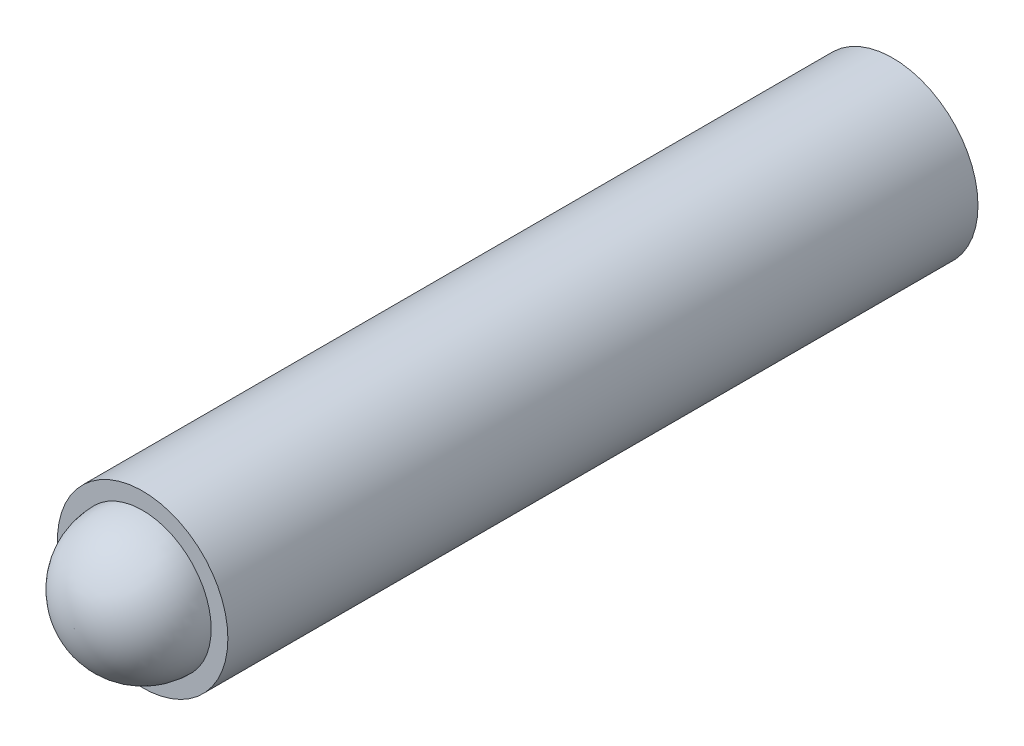
SolidWorks part; units mm, degrees
ref_plane "Front Plane" through (0, 0, 0) normal (0, 0, 1) x (1, 0, 0)
ref_plane "Top Plane" through (0, 0, 0) normal (0, 1, 0) x (1, 0, 0)
ref_plane "Right Plane" through (0, 0, 0) normal (1, 0, 0) x (0, 0, -1)
sketch "Sketch1" plane through (0, 0, 0) normal (0, 0, 1) x (1, 0, 0)
  circle A0 centre (0, 0) radius 2.5
  dimension "D1" = 5
extrude "Boss-Extrude1" add sketch "Sketch1" along normal blind 24
sketch "Sketch2" plane through (0, 0, 0) normal (0, 1, 0) x (1, 0, 0)
  line L0 (-2.5, -24) -> (2.5, -24) construction
  line L1 (2.01, -22) -> (2.5, -22)
  line L2 (2.5, -24) -> (2.5, 0) construction
  line L3 (2.5, -22) -> (2.5, -24)
  line L4 (2.5, -24) -> (0.01, -24)
  line L5 (0, -24) -> (0, -23.658) construction
  arc A0 (0.01, -24) -> (2.01, -22) centre (0.01, -22) ccw
  point P9 (0, 0)
  dimension "D1" = 2
  dimension "D2" = 0.01
revolve "Cut-Revolve6" cut sketch "Sketch2" angle 360 about L5
